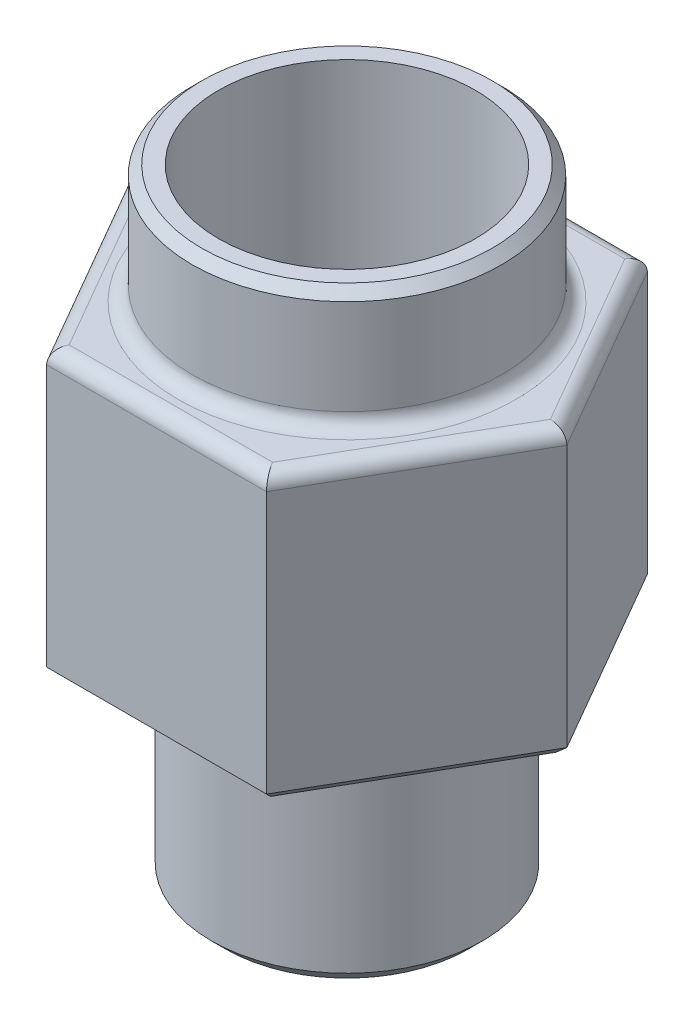
SolidWorks part; units mm, degrees
ref_plane "前视基准面" through (0, 0, 0) normal (0, 0, 1) x (1, 0, 0)
ref_plane "上视基准面" through (0, 0, 0) normal (0, 1, 0) x (1, 0, 0)
ref_plane "右视基准面" through (0, 0, 0) normal (1, 0, 0) x (0, 0, -1)
sketch "草图1" plane through (0, 0, 0) normal (0, 1, 0) x (1, 0, 0)
  circle A0 centre (0, 0) radius 2.85
  dimension "D1" = 5.7
extrude "凸台-拉伸1" add sketch "草图1" along normal blind 4.5
sketch "草图2" plane through (0, 4.5, 0) normal (0, 1, 0) x (1, 0, 0)
  line L1 (4.6188, 0) -> (2.3094, 4)
  line L2 (2.3094, 4) -> (-2.3094, 4)
  line L3 (-2.3094, 4) -> (-4.6188, 0)
  line L4 (-4.6188, 0) -> (-2.3094, -4)
  line L5 (-2.3094, -4) -> (2.3094, -4)
  line L6 (2.3094, -4) -> (4.6188, 0)
  circle A0 centre (0, 0) radius 4 construction
  dimension "D1" = 8
extrude "凸台-拉伸2" add sketch "草图2" along normal blind 6
sketch "草图3" plane through (0, 10.5, 0) normal (0, 1, 0) x (1, 0, 0)
  circle A0 centre (0, 0) radius 3.25
  dimension "D1" = 6.5
extrude "凸台-拉伸3" add sketch "草图3" along normal blind 2.5
chamfer "倒角3" distance 0.2 angle 45 7 edges at (3.4641, 4.5, -2) (0, 4.5, -4) (-3.4641, 4.5, -2) (-3.4641, 4.5, 2) (0, 4.5, 4) (3.4641, 4.5, 2) (0, 4.5, 2.85)
fillet "圆角2" radius 0.3 7 edges at (0, 10.5, 4) (-3.4641, 10.5, 2) (-3.4641, 10.5, -2) (0, 10.5, -4) (3.4641, 10.5, -2) (3.4641, 10.5, 2) (0, 10.5, 3.25)
chamfer "倒角4" distance 0.2 angle 45 1 edges at (0, 13, 3.25)
chamfer "倒角5" distance 0.3 angle 45 1 edges at (0, 0, 2.85)
sketch "草图5" plane through (0, 13, 0) normal (0, 1, 0) x (1, 0, 0)
  circle A0 centre (0, 0) radius 2.7
  dimension "D1" = 5.4
extrude "切除-拉伸1" cut sketch "草图5" against normal blind 5
